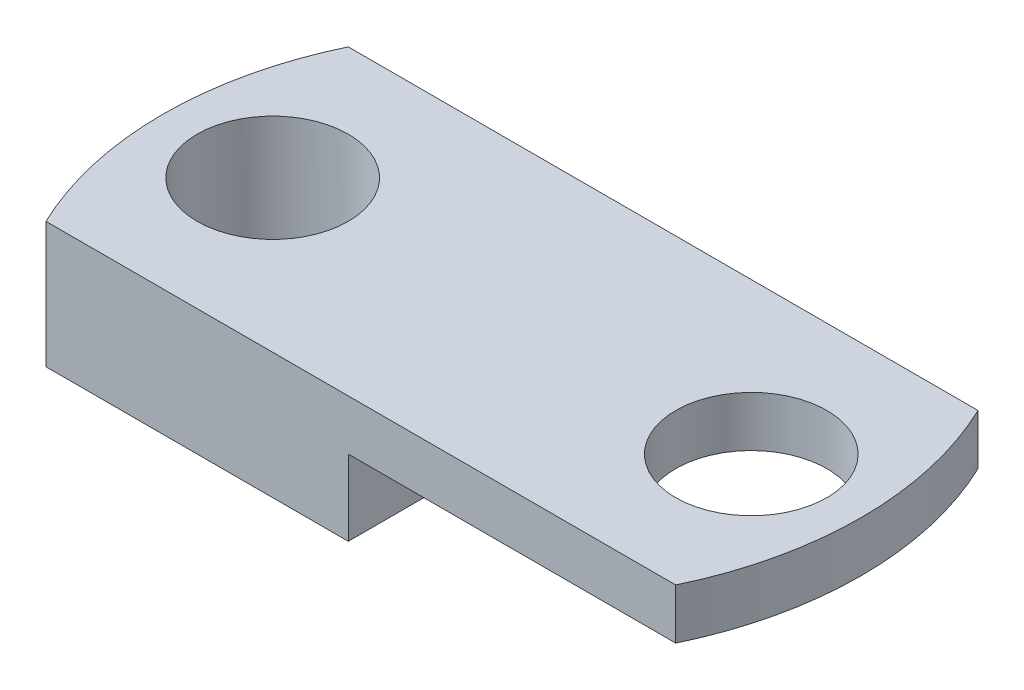
SolidWorks part; units mm, degrees
ref_plane "Front Plane" through (0, 0, 0) normal (0, 0, 1) x (1, 0, 0)
ref_plane "Top Plane" through (0, 0, 0) normal (0, 1, 0) x (1, 0, 0)
ref_plane "Right Plane" through (0, 0, 0) normal (1, 0, 0) x (0, 0, -1)
sketch "Sketch3" plane through (0, 0, 0) normal (0, 1, 0) x (1, 0, 0)
  line L1 (-15.875, 7.62) -> (15.875, 7.62)
  line L3 (-15.875, -7.62) -> (15.875, -7.62)
  line L5 (-15.875, 7.62) -> (15.875, -7.62) construction
  line L6 (-15.875, -7.62) -> (15.875, 7.62) construction
  arc A0 (-15.875, 7.62) -> (-15.875, -7.62) centre (0, 0) ccw
  arc A1 (15.875, -7.62) -> (15.875, 7.62) centre (0, 0) ccw
  point P0 (0, 0)
  dimension "D1" = 15.24
  dimension "D2" = 31.75
extrude "Boss-Extrude2" add sketch "Sketch3" along normal blind 6.35
sketch "Sketch4" plane through (0, 6.35, 0) normal (0, 1, 0) x (1, 0, 0)
  line L0 (-17.6091, 0) -> (17.6091, 0) construction
  line L1 (0, 7.62) -> (0, -7.62) construction
  line L2 (15.875, 7.62) -> (-15.875, 7.62) construction
  line L3 (-15.875, -7.62) -> (15.875, -7.62) construction
  arc A0 (-15.875, 7.62) -> (-15.875, -7.62) centre (0, 0) ccw construction
  arc A1 (15.875, -7.62) -> (15.875, 7.62) centre (0, 0) ccw construction
  circle A6 centre (12.065, 0) radius 3.81
  circle A7 centre (-12.065, 0) radius 3.81
  dimension "D1" = 24.13
  dimension "D5" = 7.62
extrude "Cut-Extrude1" cut sketch "Sketch4" against normal blind 12.7
sketch "Sketch5" plane through (0, 0, 0) normal (0, -1, 0) x (1, 0, 0)
  line L0 (15.875, -7.62) -> (-15.875, -7.62) construction
  line L1 (15.875, 7.62) -> (-0.635, 7.62)
  line L3 (15.875, -7.62) -> (-0.635, -7.62)
  line L4 (-0.635, 7.62) -> (-0.635, -7.62)
  arc A0 (15.875, 7.62) -> (15.875, -7.62) centre (0, 0) cw
  arc A1 (15.875, -7.62) -> (15.875, 7.62) centre (0, 0) ccw construction
  dimension "D1" = 16.51
extrude "Cut-Extrude2" cut sketch "Sketch5" against normal blind 3.81
